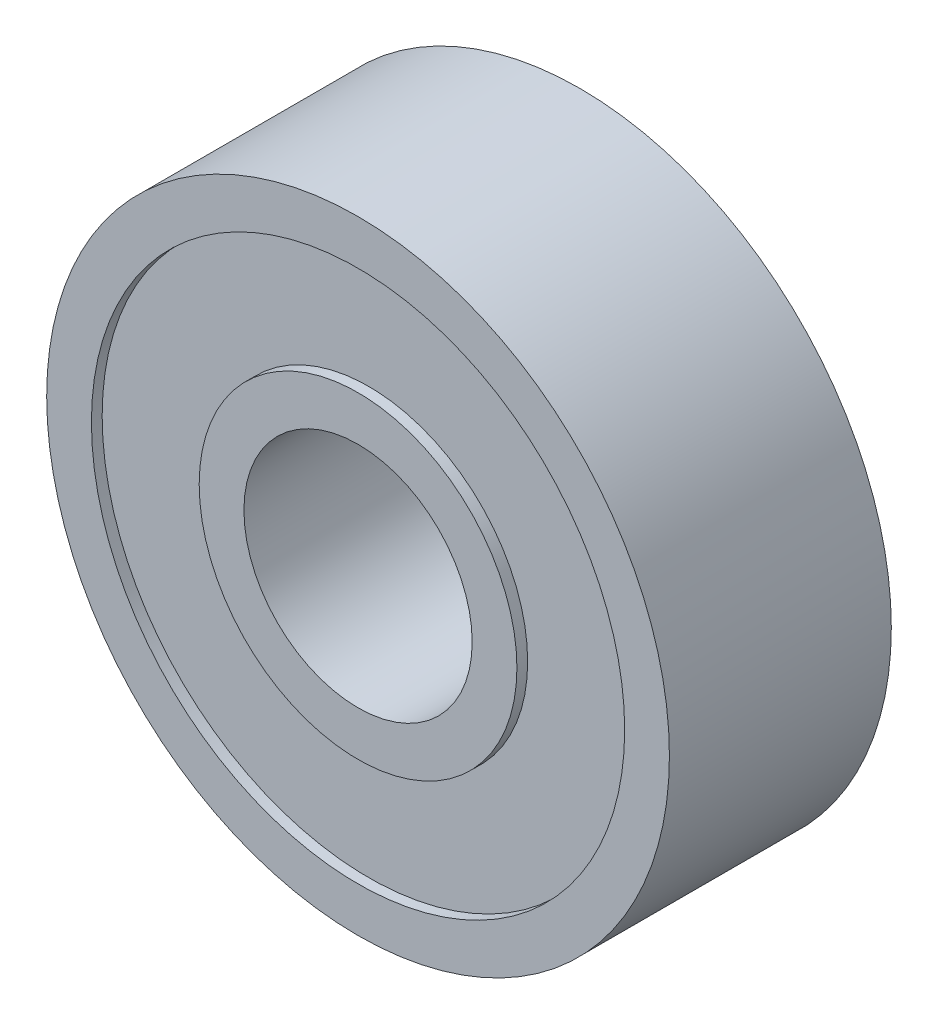
SolidWorks part; units mm, degrees
ref_plane "Front Plane" through (0, 0, 0) normal (0, 0, 1) x (1, 0, 0)
ref_plane "Top Plane" through (0, 0, 0) normal (0, 1, 0) x (1, 0, 0)
ref_plane "Right Plane" through (0, 0, 0) normal (1, 0, 0) x (0, 0, -1)
sketch "Sketch1" plane through (0, 0, 0) normal (0, 0, 1) x (1, 0, 0)
  circle A0 centre (0, 0) radius 4.05
  circle A1 centre (0, 0) radius 11.049
  dimension "D1" = 8.1
  dimension "D2" = 22.098
extrude "Boss-Extrude1" add sketch "Sketch1" along normal mid plane 7.874
sketch "Sketch2" plane through (0, 0, 3.937) normal (0, 0, 1) x (1, 0, 0)
  circle A0 centre (0, 0) radius 9.4615
  circle A1 centre (0, 0) radius 5.6375
  circle A2 centre (0, 0) radius 4.05 construction
  circle A3 centre (0, 0) radius 11.049 construction
  dimension "D1" = 1.5875
  dimension "D2" = 1.5875
extrude "Cut-Extrude1" cut sketch "Sketch2" against normal blind 0.381
mirror "Mirror1" about plane through (0, 0, 0) normal (0, 0, 1) of "Cut-Extrude1"
